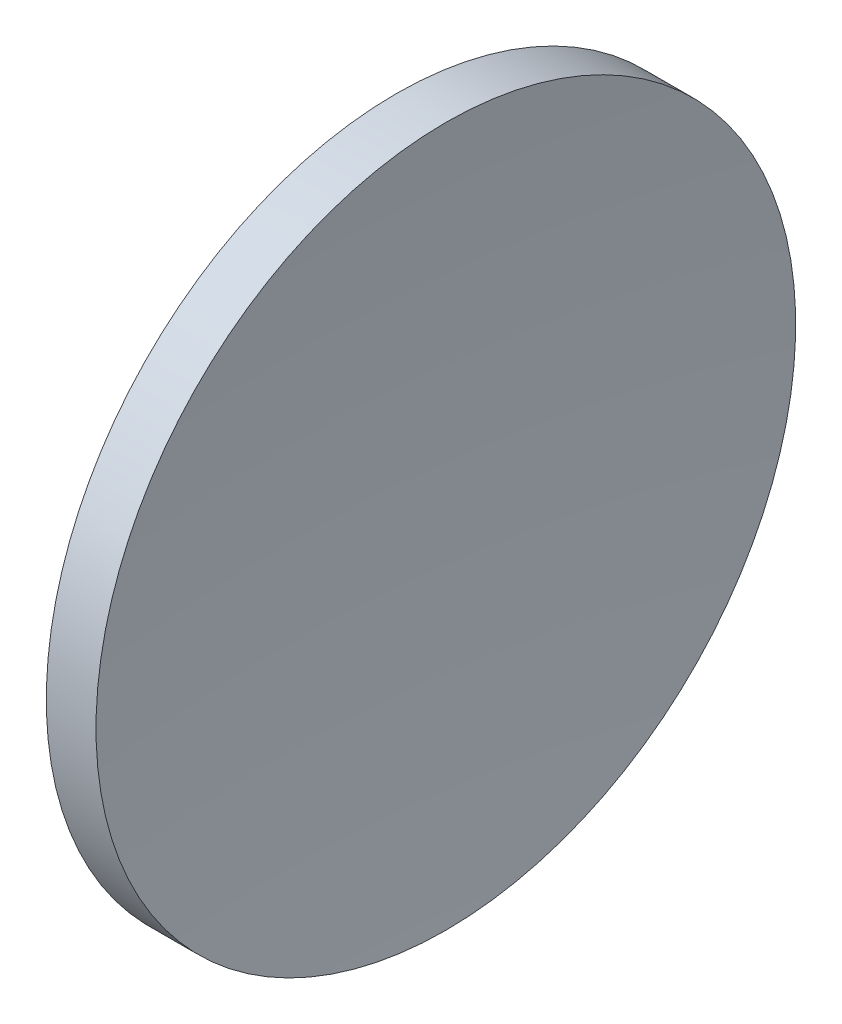
SolidWorks part; units mm, degrees
ref_plane "前视基准面" through (0, 0, 0) normal (0, 0, 1) x (1, 0, 0)
ref_plane "上视基准面" through (0, 0, 0) normal (0, 1, 0) x (1, 0, 0)
ref_plane "右视基准面" through (0, 0, 0) normal (1, 0, 0) x (0, 0, -1)
sketch "草图1" plane through (0, 0, 0) normal (0, 0, 1) x (1, 0, 0)
  line L0 (231.889, 130.4337) -> (271.8964, 130.4337) construction
  line L1 (248.8571, 155.4337) -> (252.41, 155.4337)
  line L2 (245.2821, 130.4337) -> (251.0821, 130.4337)
  arc A0 (248.8571, 155.4337) -> (245.2821, 130.4337) centre (334.4821, 130.4337) ccw
  arc A1 (252.41, 155.4337) -> (251.0821, 130.4337) centre (487.0821, 130.4337) ccw
revolve "旋转1" add sketch "草图1" angle 360 about L0
